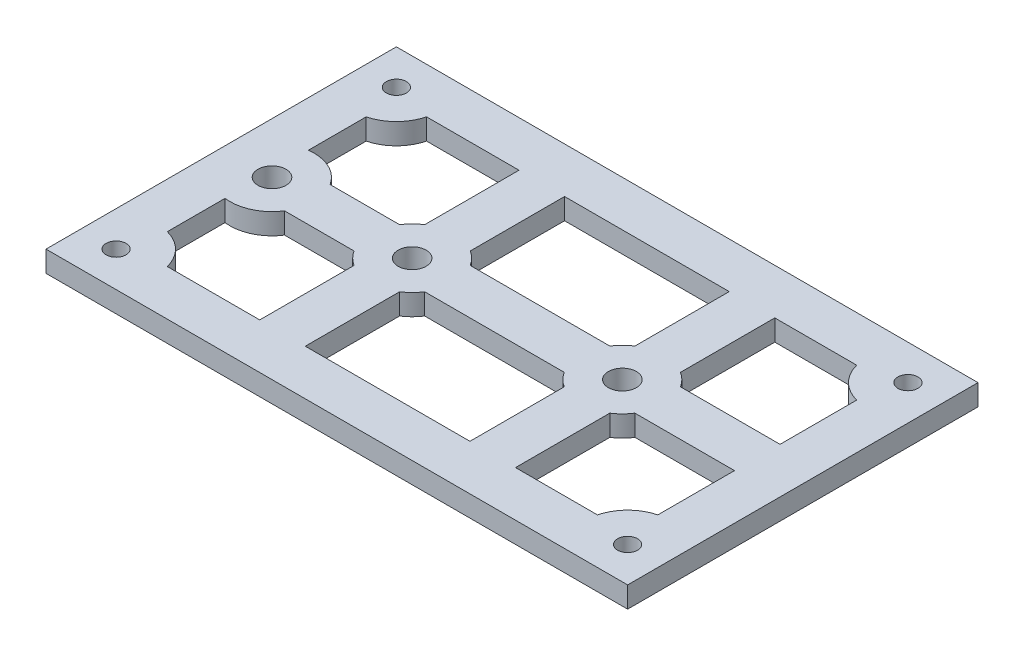
SolidWorks part; units mm, degrees
ref_plane "Front Plane" through (0, 0, 0) normal (0, 0, 1) x (1, 0, 0)
ref_plane "Top Plane" through (0, 0, 0) normal (0, 1, 0) x (1, 0, 0)
ref_plane "Right Plane" through (0, 0, 0) normal (1, 0, 0) x (0, 0, -1)
sketch "Sketch1" plane through (0, 0, 0) normal (0, 1, 0) x (1, 0, 0)
  line L1 (41.5, -25) -> (-41.5, -25)
  line L2 (41.5, -25) -> (41.5, 25)
  line L3 (41.5, 25) -> (-41.5, 25)
  line L4 (-41.5, -25) -> (-41.5, 25)
  line L5 (41.5, -25) -> (-41.5, 25) construction
  line L6 (41.5, 25) -> (-41.5, -25) construction
  point P0 (0, 0)
  dimension "D1" = 83
  dimension "D2" = 50
extrude "Boss-Extrude1" add sketch "Sketch1" along normal blind 3
sketch "Sketch2" plane through (0, 0, 0) normal (0, -1, 0) x (1, 0, 0)
  line L1 (-68.8144, 0) -> (82.9515, 0) construction
  line L2 (-41.5, -25) -> (-41.5, 25) construction
  circle A0 centre (-34.25, 0) radius 2
  circle A1 centre (-14.25, 0) radius 2
  circle A2 centre (15.75, 0) radius 2
  dimension "D1" = 4
  dimension "D2" = 20
  dimension "D3" = 30
  dimension "D4" = 7.25
extrude "Cut-Extrude1" cut sketch "Sketch2" against normal through all
sketch "Sketch3" plane through (0, 0, 0) normal (0, -1, 0) x (1, 0, 0)
  line L0 (41.5, -25) -> (-41.5, -25) construction
  line L1 (-41.5, -25) -> (-41.5, 25) construction
  circle A0 centre (-36.5, -20) radius 1.425
  dimension "D1" = 2.85
  dimension "D2" = 5
  dimension "D3" = 5
extrude "Cut-Extrude2" cut sketch "Sketch3" against normal through all
pattern_linear "LPattern1" count 2 spacing 73 along (1, 0, 0) count 2 spacing 40 along (0, 0, 1) of "Cut-Extrude2"
sketch "Sketch4" plane through (0, 0, 0) normal (0, -1, 0) x (1, 0, 0)
  line L0 (0, 43.3094) -> (0, 18.5) construction
  line L1 (-77.2575, 0) -> (100.12, 0) construction
  line L2 (-11, 18.5) -> (-30.6905, 18.5) construction
  line L3 (0, 18.5) -> (-11, 18.5)
  line L5 (0, 3.25) -> (-9.2064, 3.25)
  line L6 (-11, 18.5) -> (-11, 5.0436)
  line L7 (0, -3.25) -> (-9.2064, -3.25)
  line L9 (0, -18.5) -> (-11, -18.5)
  line L10 (-11, -5.0436) -> (-11, -18.5)
  line L11 (-17.5, 18.5) -> (-30.6905, 18.5)
  line L12 (-17.5, 18.5) -> (-17.5, 5.0436)
  line L13 (-19.2936, 3.25) -> (-29.2064, 3.25)
  line L14 (-35, 14.1905) -> (-35, 5.9529)
  line L15 (-19.2936, -3.25) -> (-29.2064, -3.25)
  line L16 (-17.5, -5.0436) -> (-17.5, -18.5)
  line L17 (-17.5, -18.5) -> (-30.6905, -18.5)
  line L18 (-35, -5.9529) -> (-35, -14.1905)
  line L19 (-11, -18.5) -> (-30.6905, -18.5) construction
  line L20 (-41.5, 25) -> (41.5, 25) construction
  line L21 (-45.8095, 18.5) -> (-49.6813, 18.5) construction
  line L22 (-41.5, -25) -> (-41.5, 25) construction
  line L23 (41.5, 25) -> (41.5, -25) construction
  line L24 (-14.25, 42.3273) -> (-14.25, -40.9224) construction
  line L25 (0, 18.5) -> (12.5, 18.5)
  line L27 (0, 3.25) -> (10.7064, 3.25)
  line L28 (12.5, 18.5) -> (12.5, 5.0436)
  line L29 (0, -3.25) -> (10.7064, -3.25)
  line L31 (0, -18.5) -> (12.5, -18.5)
  line L32 (12.5, -5.0436) -> (12.5, -18.5)
  line L33 (20.7936, 3.25) -> (35, 3.25)
  line L34 (19, 5.0436) -> (19, 18.5)
  line L35 (19, 18.5) -> (30.6905, 18.5)
  line L36 (35, 3.25) -> (35, 14.1905)
  line L37 (20.7936, -3.25) -> (35, -3.25)
  line L38 (19, -5.0436) -> (19, -18.5)
  line L39 (19, -18.5) -> (30.6905, -18.5)
  line L40 (35, -3.25) -> (35, -14.1905)
  line L41 (15.75, -31.8218) -> (15.75, 53.5391) construction
  line L42 (0, 3.25) -> (0, -3.25) construction
  line L43 (0, -18.5) -> (0, -46.3088) construction
  arc A0 (-35, 14.1905) -> (-30.6905, 18.5) centre (-36.5, 20) ccw
  arc A1 (-35, -5.9529) -> (-29.2064, -3.25) centre (-34.25, 0) ccw
  arc A2 (-30.6905, -18.5) -> (-35, -14.1905) centre (-36.5, -20) ccw
  arc A3 (-19.2936, -3.25) -> (-17.5, -5.0436) centre (-14.25, 0) ccw
  arc A4 (-29.2064, 3.25) -> (-35, 5.9529) centre (-34.25, 0) ccw
  arc A5 (-17.5, 5.0436) -> (-19.2936, 3.25) centre (-14.25, 0) ccw
  arc A6 (-9.2064, 3.25) -> (-11, 5.0436) centre (-14.25, 0) ccw
  arc A7 (-11, -5.0436) -> (-9.2064, -3.25) centre (-14.25, 0) ccw
  arc A8 (35, -14.1905) -> (30.6905, -18.5) centre (36.5, -20) ccw
  arc A9 (30.6905, 18.5) -> (35, 14.1905) centre (36.5, 20) ccw
  arc A10 (19, -5.0436) -> (20.7936, -3.25) centre (15.75, 0) ccw
  arc A11 (10.7064, -3.25) -> (12.5, -5.0436) centre (15.75, 0) ccw
  arc A12 (12.5, 5.0436) -> (10.7064, 3.25) centre (15.75, 0) ccw
  arc A13 (20.7936, 3.25) -> (19, 5.0436) centre (15.75, 0) ccw
  dimension "D7" = 12
  dimension "D3" = 6
  dimension "D8" = 6
  dimension "D14" = 6
  dimension "D15" = 6
  dimension "D16" = 6
  dimension "D1" = 6.5
  dimension "D2" = 6.5
  dimension "D4" = 6.5
  dimension "D5" = 6.5
  dimension "D6" = 6.5
  dimension "D9" = 9.9129
  dimension "D10" = 6.5
  dimension "D11" = 6.5
  dimension "D12" = 6.5
  dimension "D13" = 6.5
  dimension "D17" = 13.4564
extrude "Cut-Extrude3" cut sketch "Sketch4" against normal blind 10
